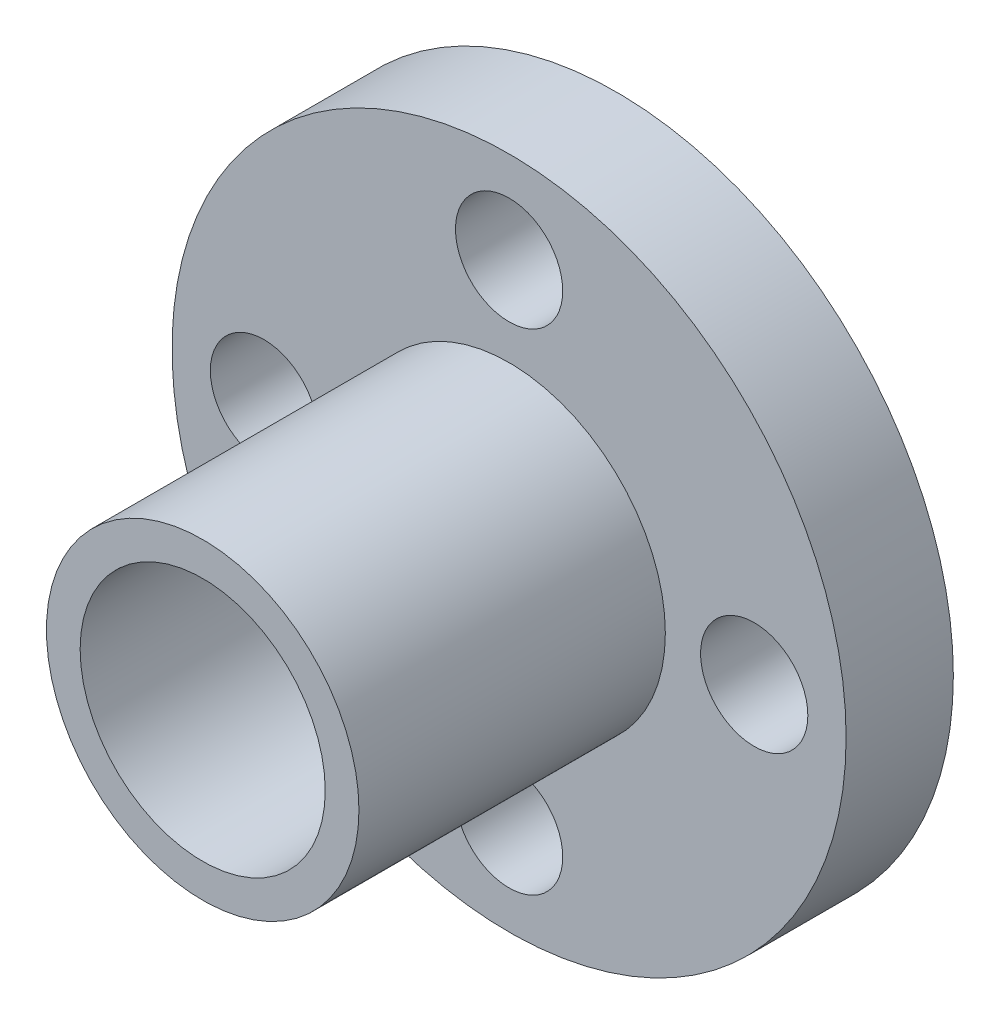
SolidWorks part; units mm, degrees
ref_plane "Plan de face" through (0, 0, 0) normal (0, 0, 1) x (1, 0, 0)
ref_plane "Plan de dessus" through (0, 0, 0) normal (0, 1, 0) x (1, 0, 0)
ref_plane "Plan de droite" through (0, 0, 0) normal (1, 0, 0) x (0, 0, -1)
sketch "Sketch1" plane through (0, 0, 0) normal (0, 0, 1) x (1, 0, 0)
  circle A0 centre (0, 0) radius 11
  dimension "D2" = 22
extrude "Boss-Extrude1" add sketch "Sketch1" along normal blind 3.5
sketch "Sketch2" plane through (0, 0, 3.5) normal (0, 0, 1) x (1, 0, 0)
  circle A0 centre (0, 0) radius 4
  dimension "D1" = 8
extrude "Cut-Extrude3" cut sketch "Sketch2" against normal through all
sketch "Sketch7" plane through (0, 0, 3.5) normal (0, 0, 1) x (1, 0, 0)
  circle A0 centre (0, 0) radius 5.1
  circle A1 centre (0, 0) radius 4
  dimension "D1" = 8
  dimension "D2" = 10.2
extrude "Boss-Extrude3" add sketch "Sketch7" against normal blind 5 and the other way blind 10
sketch "Sketch10" plane through (0, 0, 3.5) normal (0, 0, 1) x (1, 0, 0)
  line L0 (0, 0) -> (8, 0) construction
  line L1 (0, 0) -> (0, -8) construction
  circle A0 centre (8, 0) radius 1.75
  circle A1 centre (0, -8) radius 1.75
  circle A2 centre (0, 8) radius 1.75
  circle A3 centre (-8, 0) radius 1.75
  dimension "D3" = 3.5
  dimension "D4" = 3.5
  dimension "D1" = 8
  dimension "D2" = 8
extrude "Cut-Extrude4" cut sketch "Sketch10" against normal through all
